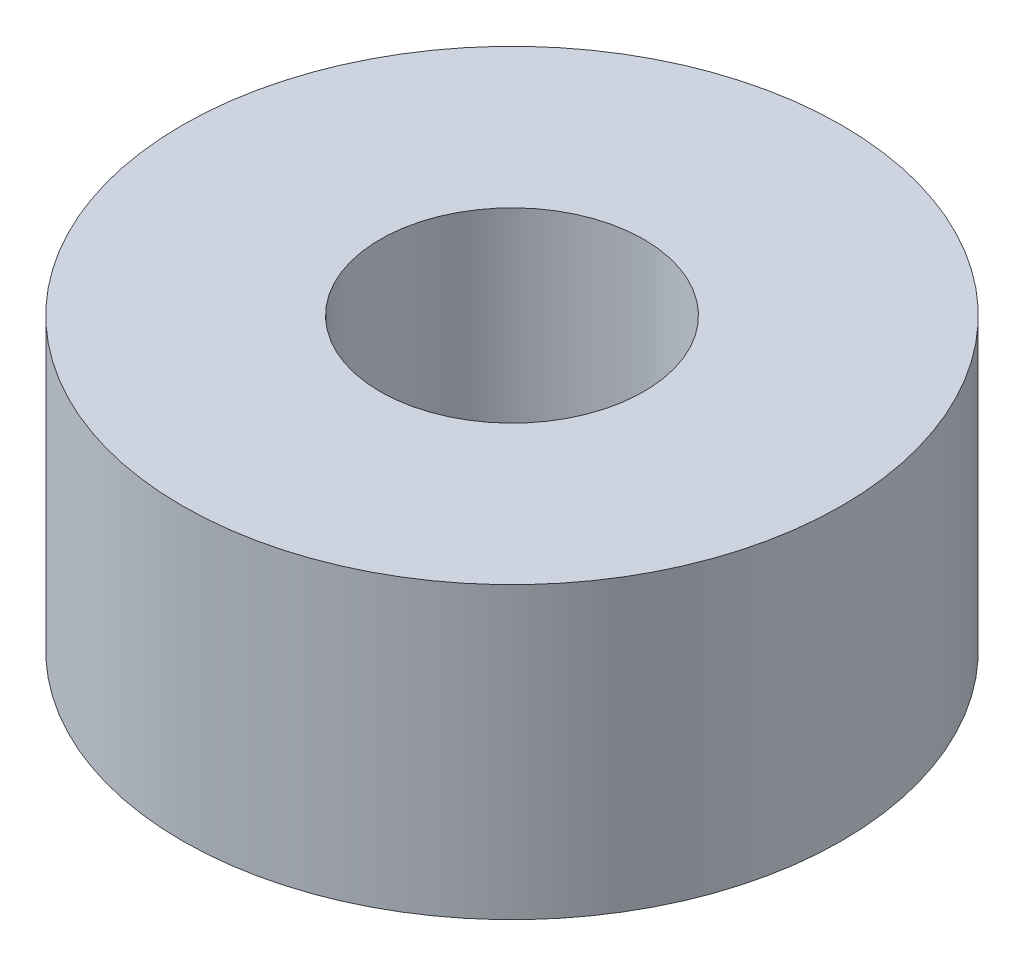
SolidWorks part; units mm, degrees
ref_plane "Front Plane" through (0, 0, 0) normal (0, 0, 1) x (1, 0, 0)
ref_plane "Top Plane" through (0, 0, 0) normal (0, 1, 0) x (1, 0, 0)
ref_plane "Right Plane" through (0, 0, 0) normal (1, 0, 0) x (0, 0, -1)
sketch "Sketch1" plane through (0, 0, 0) normal (0, 1, 0) x (1, 0, 0)
  circle A0 centre (0, 0) radius 2.5
  circle A1 centre (0, 0) radius 1
  dimension "D1" = 2
  dimension "D2" = 5
extrude "Boss-Extrude1" add sketch "Sketch1" along normal blind 2.2
